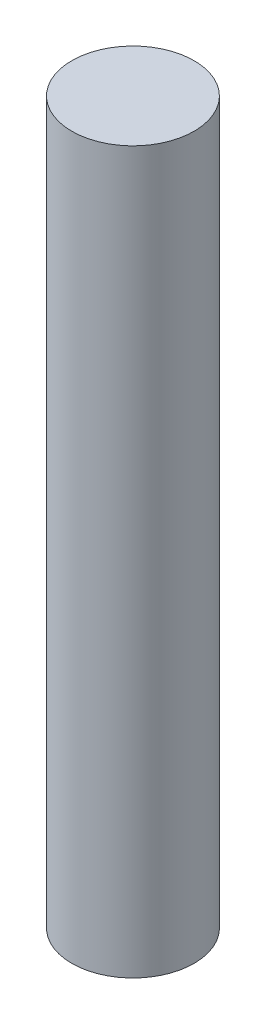
SolidWorks part; units mm, degrees
ref_plane "Front Plane" through (0, 0, 0) normal (0, 0, 1) x (1, 0, 0)
ref_plane "Top Plane" through (0, 0, 0) normal (0, 1, 0) x (1, 0, 0)
ref_plane "Right Plane" through (0, 0, 0) normal (1, 0, 0) x (0, 0, -1)
sketch "Sketch1" plane through (0, 0, 0) normal (0, 1, 0) x (1, 0, 0)
  circle A0 centre (0, 0) radius 6
  dimension "D1" = 12
extrude "Boss-Extrude1" add sketch "Sketch1" along normal blind 70.7
